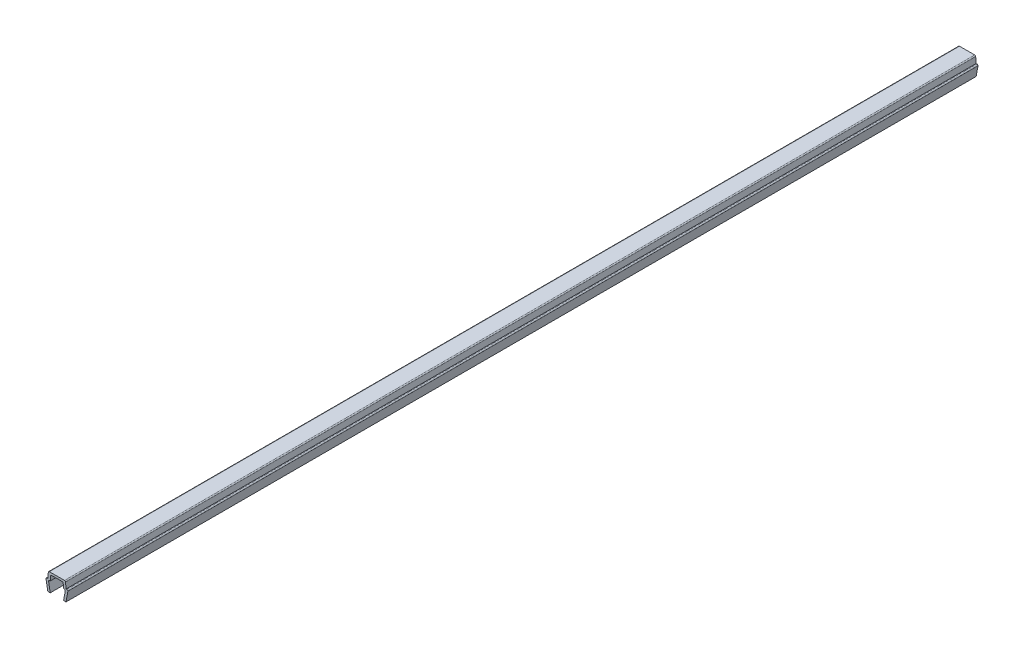
SolidWorks part; units mm, degrees
ref_plane "Front Plane" through (0, 0, 0) normal (0, 0, 1) x (1, 0, 0)
ref_plane "Top Plane" through (0, 0, 0) normal (0, 1, 0) x (1, 0, 0)
ref_plane "Right Plane" through (0, 0, 0) normal (1, 0, 0) x (0, 0, -1)
ref_plane "Plane1" through (0, 0, 0) normal (0, 0, 1) x (1, 0, 0)
sketch "Sketch1" plane through (0, 0, 0) normal (0, 0, 1) x (1, 0, 0)
  line L0 (-3.6, 3.35) -> (-3, 0)
  line L1 (-3, 0) -> (-2.2, 0)
  line L2 (-2.2, 0) -> (-2.7352, 2.9883)
  line L3 (-2.3907, 3.4) -> (-2.2, 3.4)
  line L4 (-2.2, 3.4) -> (-2.0705, 4.8805)
  line L5 (-1.7218, 5.2) -> (1.7218, 5.2)
  line L6 (2.0705, 4.8805) -> (2.2, 3.4)
  line L7 (2.2, 3.4) -> (2.3907, 3.4)
  line L8 (2.7352, 2.9883) -> (2.2, 0)
  line L9 (2.2, 0) -> (3, 0)
  line L10 (3, 0) -> (3.6, 3.35)
  line L11 (3.25, 3.7) -> (3, 3.7)
  line L12 (3, 3.7) -> (2.8355, 5.5805)
  line L13 (2.4868, 5.9) -> (-2.4868, 5.9)
  line L14 (-2.8355, 5.5805) -> (-3, 3.7)
  line L15 (-3, 3.7) -> (-3.25, 3.7)
  arc A0 (-2.7352, 2.9883) -> (-2.3907, 3.4) centre (-2.3907, 3.05) cw
  arc A1 (-2.0705, 4.8805) -> (-1.7218, 5.2) centre (-1.7218, 4.85) cw
  arc A2 (1.7218, 5.2) -> (2.0705, 4.8805) centre (1.7218, 4.85) cw
  arc A3 (2.3907, 3.4) -> (2.7352, 2.9883) centre (2.3907, 3.05) cw
  arc A4 (3.6, 3.35) -> (3.25, 3.7) centre (3.25, 3.35) ccw
  arc A5 (2.8355, 5.5805) -> (2.4868, 5.9) centre (2.4868, 5.55) ccw
  arc A6 (-2.4868, 5.9) -> (-2.8355, 5.5805) centre (-2.4868, 5.55) ccw
  arc A7 (-3.25, 3.7) -> (-3.6, 3.35) centre (-3.25, 3.35) ccw
extrude "Boss-Extrude1" add sketch "Sketch1" against normal mid plane 300
